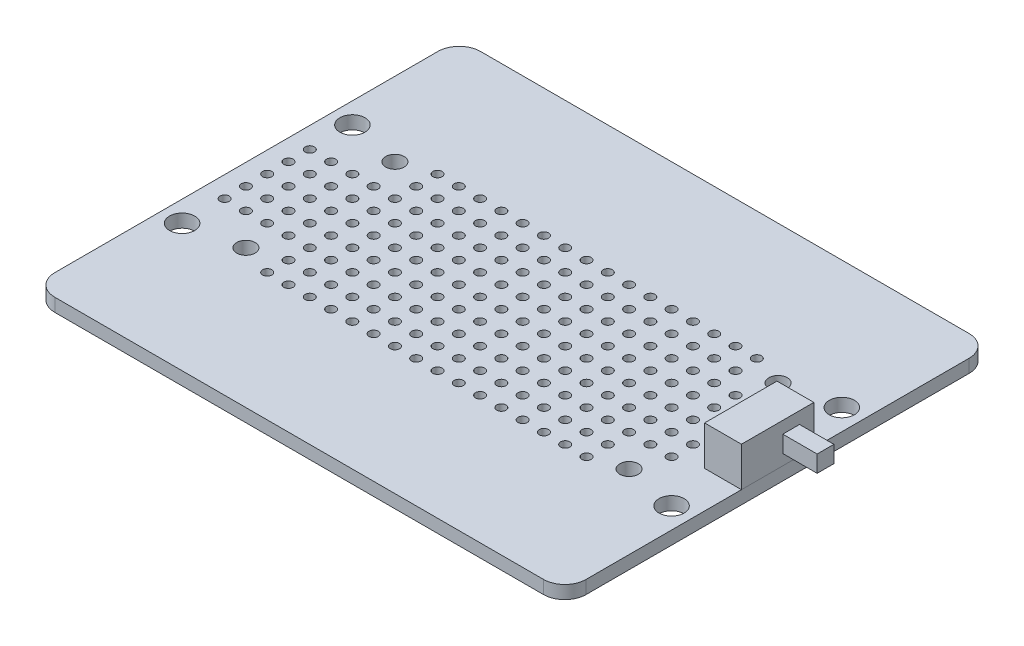
SolidWorks part; units mm, degrees
ref_plane "Front" through (0, 0, 0) normal (0, 0, 1) x (1, 0, 0)
ref_plane "Top" through (0, 0, 0) normal (0, 1, 0) x (1, 0, 0)
ref_plane "Right" through (0, 0, 0) normal (1, 0, 0) x (0, 0, -1)
sketch "Sketch1" plane through (0, 0, 0) normal (0, 1, 0) x (1, 0, 0)
  line L0 (29.2, 10.16) -> (29.2, -10.16) construction
  line L1 (-31.7, 25.4) -> (31.7, 25.4)
  line L2 (-31.7, 25.4) -> (-31.7, -25.4)
  line L3 (-31.7, -25.4) -> (31.7, -25.4)
  line L4 (31.7, 25.4) -> (31.7, -25.4)
  line L5 (-31.7, 25.4) -> (31.7, -25.4) construction
  line L6 (-31.7, -25.4) -> (31.7, 25.4) construction
  line L7 (29.2, 0) -> (0, 0) construction
  line L8 (-29.2, 10.16) -> (-29.2, -10.16) construction
  line L9 (-29.2, 0) -> (0, 0) construction
  line L10 (-22.86, 8.89) -> (-22.86, -8.89) construction
  line L11 (22.86, 8.89) -> (22.86, -8.89) construction
  line L12 (-22.86, 0) -> (22.86, 0) construction
  circle A0 centre (29.2, 10.16) radius 1.5
  circle A1 centre (29.2, -10.16) radius 1.5
  circle A2 centre (-29.2, 10.16) radius 1.5
  circle A3 centre (-29.2, -10.16) radius 1.5
  circle A4 centre (-22.86, 8.89) radius 1.1
  circle A5 centre (-22.86, -8.89) radius 1.1
  circle A6 centre (22.86, -8.89) radius 1.1
  circle A7 centre (22.86, 8.89) radius 1.1
  point P0 (0, 0)
  point P29 (0, 0)
  dimension "D3" = 3
  dimension "D4" = 20.32
  dimension "D5" = 55.4
  dimension "D6" = 2.2
  dimension "D1" = 50.8
  dimension "D2" = 63.4
  dimension "D7" = 45.72
  dimension "D8" = 17.78
  dimension "D9" = 17.78
extrude "Boss-Extrude1" add sketch "Sketch1" along normal blind 1.57
sketch "Sketch9" plane through (0, 0, 0) normal (0, 1, 0) x (1, 0, 0)
  line L0 (-29.21, 10.16) -> (-26.67, 10.16) construction
  line L1 (-29.21, 10.16) -> (-29.21, 7.62) construction
  line L2 (-29.21, 10.16) -> (24.13, 10.16) construction
  line L3 (24.13, 10.16) -> (24.13, -10.16) construction
  line L4 (24.13, -10.16) -> (-29.21, -10.16) construction
  line L5 (-29.21, -10.16) -> (-29.21, 10.16) construction
  line L6 (-2.54, 10.16) -> (-2.54, -10.16) construction
  line L7 (-29.21, 0) -> (24.13, 0) construction
  circle A0 centre (-29.21, 10.16) radius 0.55
  circle A1 centre (-26.67, 10.16) radius 0.55 [skipped]
  circle A2 centre (-24.13, 10.16) radius 0.55 [skipped]
  circle A3 centre (-21.59, 10.16) radius 0.55 [skipped]
  circle A4 centre (-19.05, 10.16) radius 0.55
  circle A5 centre (-16.51, 10.16) radius 0.55
  circle A6 centre (-13.97, 10.16) radius 0.55
  circle A7 centre (-11.43, 10.16) radius 0.55
  circle A8 centre (-8.89, 10.16) radius 0.55
  circle A9 centre (-6.35, 10.16) radius 0.55
  circle A10 centre (-3.81, 10.16) radius 0.55
  circle A11 centre (-1.27, 10.16) radius 0.55
  circle A12 centre (1.27, 10.16) radius 0.55
  circle A13 centre (3.81, 10.16) radius 0.55
  circle A14 centre (6.35, 10.16) radius 0.55
  circle A15 centre (8.89, 10.16) radius 0.55
  circle A16 centre (11.43, 10.16) radius 0.55
  circle A17 centre (13.97, 10.16) radius 0.55
  circle A18 centre (16.51, 10.16) radius 0.55
  circle A19 centre (19.05, 10.16) radius 0.55
  circle A20 centre (21.59, 10.16) radius 0.55 [skipped]
  circle A21 centre (24.13, 10.16) radius 0.55 [skipped]
  circle A22 centre (26.67, 10.16) radius 0.55 [skipped]
  circle A23 centre (29.21, 10.16) radius 0.55 [skipped]
  circle A24 centre (-26.67, 7.62) radius 0.55 [skipped]
  circle A25 centre (-24.13, 7.62) radius 0.55 [skipped]
  circle A26 centre (-21.59, 7.62) radius 0.55 [skipped]
  circle A27 centre (-19.05, 7.62) radius 0.55
  circle A28 centre (-16.51, 7.62) radius 0.55
  circle A29 centre (-13.97, 7.62) radius 0.55
  circle A30 centre (-11.43, 7.62) radius 0.55
  circle A31 centre (-8.89, 7.62) radius 0.55
  circle A32 centre (-6.35, 7.62) radius 0.55
  circle A33 centre (-3.81, 7.62) radius 0.55
  circle A34 centre (-1.27, 7.62) radius 0.55
  circle A35 centre (1.27, 7.62) radius 0.55
  circle A36 centre (3.81, 7.62) radius 0.55
  circle A37 centre (6.35, 7.62) radius 0.55
  circle A38 centre (8.89, 7.62) radius 0.55
  circle A39 centre (11.43, 7.62) radius 0.55
  circle A40 centre (13.97, 7.62) radius 0.55
  circle A41 centre (16.51, 7.62) radius 0.55
  circle A42 centre (19.05, 7.62) radius 0.55
  circle A43 centre (21.59, 7.62) radius 0.55 [skipped]
  circle A44 centre (24.13, 7.62) radius 0.55 [skipped]
  circle A45 centre (26.67, 7.62) radius 0.55 [skipped]
  circle A46 centre (29.21, 7.62) radius 0.55 [skipped]
  circle A47 centre (-26.67, 5.08) radius 0.55
  circle A48 centre (-24.13, 5.08) radius 0.55
  circle A49 centre (-21.59, 5.08) radius 0.55
  circle A50 centre (-19.05, 5.08) radius 0.55
  circle A51 centre (-16.51, 5.08) radius 0.55
  circle A52 centre (-13.97, 5.08) radius 0.55
  circle A53 centre (-11.43, 5.08) radius 0.55
  circle A54 centre (-8.89, 5.08) radius 0.55
  circle A55 centre (-6.35, 5.08) radius 0.55
  circle A56 centre (-3.81, 5.08) radius 0.55
  circle A57 centre (-1.27, 5.08) radius 0.55
  circle A58 centre (1.27, 5.08) radius 0.55
  circle A59 centre (3.81, 5.08) radius 0.55
  circle A60 centre (6.35, 5.08) radius 0.55
  circle A61 centre (8.89, 5.08) radius 0.55
  circle A62 centre (11.43, 5.08) radius 0.55
  circle A63 centre (13.97, 5.08) radius 0.55
  circle A64 centre (16.51, 5.08) radius 0.55
  circle A65 centre (19.05, 5.08) radius 0.55
  circle A66 centre (21.59, 5.08) radius 0.55
  circle A67 centre (24.13, 5.08) radius 0.55
  circle A68 centre (26.67, 5.08) radius 0.55 [skipped]
  circle A69 centre (29.21, 5.08) radius 0.55 [skipped]
  circle A70 centre (-26.67, 2.54) radius 0.55
  circle A71 centre (-24.13, 2.54) radius 0.55
  circle A72 centre (-21.59, 2.54) radius 0.55
  circle A73 centre (-19.05, 2.54) radius 0.55
  circle A74 centre (-16.51, 2.54) radius 0.55
  circle A75 centre (-13.97, 2.54) radius 0.55
  circle A76 centre (-11.43, 2.54) radius 0.55
  circle A77 centre (-8.89, 2.54) radius 0.55
  circle A78 centre (-6.35, 2.54) radius 0.55
  circle A79 centre (-3.81, 2.54) radius 0.55
  circle A80 centre (-1.27, 2.54) radius 0.55
  circle A81 centre (1.27, 2.54) radius 0.55
  circle A82 centre (3.81, 2.54) radius 0.55
  circle A83 centre (6.35, 2.54) radius 0.55
  circle A84 centre (8.89, 2.54) radius 0.55
  circle A85 centre (11.43, 2.54) radius 0.55
  circle A86 centre (13.97, 2.54) radius 0.55
  circle A87 centre (16.51, 2.54) radius 0.55
  circle A88 centre (19.05, 2.54) radius 0.55
  circle A89 centre (21.59, 2.54) radius 0.55
  circle A90 centre (24.13, 2.54) radius 0.55
  circle A91 centre (26.67, 2.54) radius 0.55 [skipped]
  circle A92 centre (29.21, 2.54) radius 0.55 [skipped]
  circle A93 centre (-26.67, 0) radius 0.55
  circle A94 centre (-24.13, 0) radius 0.55
  circle A95 centre (-21.59, 0) radius 0.55
  circle A96 centre (-19.05, 0) radius 0.55
  circle A97 centre (-16.51, 0) radius 0.55
  circle A98 centre (-13.97, 0) radius 0.55
  circle A99 centre (-11.43, 0) radius 0.55
  circle A100 centre (-8.89, 0) radius 0.55
  circle A101 centre (-6.35, 0) radius 0.55
  circle A102 centre (-3.81, 0) radius 0.55
  circle A103 centre (-1.27, 0) radius 0.55
  circle A104 centre (1.27, 0) radius 0.55
  circle A105 centre (3.81, 0) radius 0.55
  circle A106 centre (6.35, 0) radius 0.55
  circle A107 centre (8.89, 0) radius 0.55
  circle A108 centre (11.43, 0) radius 0.55
  circle A109 centre (13.97, 0) radius 0.55
  circle A110 centre (16.51, 0) radius 0.55
  circle A111 centre (19.05, 0) radius 0.55
  circle A112 centre (21.59, 0) radius 0.55
  circle A113 centre (24.13, 0) radius 0.55
  circle A114 centre (26.67, 0) radius 0.55 [skipped]
  circle A115 centre (29.21, 0) radius 0.55 [skipped]
  circle A116 centre (-26.67, -2.54) radius 0.55
  circle A117 centre (-24.13, -2.54) radius 0.55
  circle A118 centre (-21.59, -2.54) radius 0.55
  circle A119 centre (-19.05, -2.54) radius 0.55
  circle A120 centre (-16.51, -2.54) radius 0.55
  circle A121 centre (-13.97, -2.54) radius 0.55
  circle A122 centre (-11.43, -2.54) radius 0.55
  circle A123 centre (-8.89, -2.54) radius 0.55
  circle A124 centre (-6.35, -2.54) radius 0.55
  circle A125 centre (-3.81, -2.54) radius 0.55
  circle A126 centre (-1.27, -2.54) radius 0.55
  circle A127 centre (1.27, -2.54) radius 0.55
  circle A128 centre (3.81, -2.54) radius 0.55
  circle A129 centre (6.35, -2.54) radius 0.55
  circle A130 centre (8.89, -2.54) radius 0.55
  circle A131 centre (11.43, -2.54) radius 0.55
  circle A132 centre (13.97, -2.54) radius 0.55
  circle A133 centre (16.51, -2.54) radius 0.55
  circle A134 centre (19.05, -2.54) radius 0.55
  circle A135 centre (21.59, -2.54) radius 0.55
  circle A136 centre (24.13, -2.54) radius 0.55
  circle A137 centre (26.67, -2.54) radius 0.55 [skipped]
  circle A138 centre (29.21, -2.54) radius 0.55 [skipped]
  circle A139 centre (-26.67, -5.08) radius 0.55
  circle A140 centre (-24.13, -5.08) radius 0.55
  circle A141 centre (-21.59, -5.08) radius 0.55
  circle A142 centre (-19.05, -5.08) radius 0.55
  circle A143 centre (-16.51, -5.08) radius 0.55
  circle A144 centre (-13.97, -5.08) radius 0.55
  circle A145 centre (-11.43, -5.08) radius 0.55
  circle A146 centre (-8.89, -5.08) radius 0.55
  circle A147 centre (-6.35, -5.08) radius 0.55
  circle A148 centre (-3.81, -5.08) radius 0.55
  circle A149 centre (-1.27, -5.08) radius 0.55
  circle A150 centre (1.27, -5.08) radius 0.55
  circle A151 centre (3.81, -5.08) radius 0.55
  circle A152 centre (6.35, -5.08) radius 0.55
  circle A153 centre (8.89, -5.08) radius 0.55
  circle A154 centre (11.43, -5.08) radius 0.55
  circle A155 centre (13.97, -5.08) radius 0.55
  circle A156 centre (16.51, -5.08) radius 0.55
  circle A157 centre (19.05, -5.08) radius 0.55
  circle A158 centre (21.59, -5.08) radius 0.55
  circle A159 centre (24.13, -5.08) radius 0.55
  circle A160 centre (26.67, -5.08) radius 0.55 [skipped]
  circle A161 centre (29.21, -5.08) radius 0.55 [skipped]
  circle A162 centre (-26.67, -7.62) radius 0.55 [skipped]
  circle A163 centre (-24.13, -7.62) radius 0.55 [skipped]
  circle A164 centre (-21.59, -7.62) radius 0.55 [skipped]
  circle A165 centre (-19.05, -7.62) radius 0.55
  circle A166 centre (-16.51, -7.62) radius 0.55
  circle A167 centre (-13.97, -7.62) radius 0.55
  circle A168 centre (-11.43, -7.62) radius 0.55
  circle A169 centre (-8.89, -7.62) radius 0.55
  circle A170 centre (-6.35, -7.62) radius 0.55
  circle A171 centre (-3.81, -7.62) radius 0.55
  circle A172 centre (-1.27, -7.62) radius 0.55
  circle A173 centre (1.27, -7.62) radius 0.55
  circle A174 centre (3.81, -7.62) radius 0.55
  circle A175 centre (6.35, -7.62) radius 0.55
  circle A176 centre (8.89, -7.62) radius 0.55
  circle A177 centre (11.43, -7.62) radius 0.55
  circle A178 centre (13.97, -7.62) radius 0.55
  circle A179 centre (16.51, -7.62) radius 0.55
  circle A180 centre (19.05, -7.62) radius 0.55
  circle A181 centre (21.59, -7.62) radius 0.55 [skipped]
  circle A182 centre (24.13, -7.62) radius 0.55 [skipped]
  circle A183 centre (26.67, -7.62) radius 0.55 [skipped]
  circle A184 centre (29.21, -7.62) radius 0.55 [skipped]
  circle A185 centre (-26.67, -10.16) radius 0.55 [skipped]
  circle A186 centre (-24.13, -10.16) radius 0.55 [skipped]
  circle A187 centre (-21.59, -10.16) radius 0.55 [skipped]
  circle A188 centre (-19.05, -10.16) radius 0.55
  circle A189 centre (-16.51, -10.16) radius 0.55
  circle A190 centre (-13.97, -10.16) radius 0.55
  circle A191 centre (-11.43, -10.16) radius 0.55
  circle A192 centre (-8.89, -10.16) radius 0.55
  circle A193 centre (-6.35, -10.16) radius 0.55
  circle A194 centre (-3.81, -10.16) radius 0.55
  circle A195 centre (-1.27, -10.16) radius 0.55
  circle A196 centre (1.27, -10.16) radius 0.55
  circle A197 centre (3.81, -10.16) radius 0.55
  circle A198 centre (6.35, -10.16) radius 0.55
  circle A199 centre (8.89, -10.16) radius 0.55
  circle A200 centre (11.43, -10.16) radius 0.55
  circle A201 centre (13.97, -10.16) radius 0.55
  circle A202 centre (16.51, -10.16) radius 0.55
  circle A203 centre (19.05, -10.16) radius 0.55
  circle A204 centre (21.59, -10.16) radius 0.55 [skipped]
  circle A205 centre (24.13, -10.16) radius 0.55 [skipped]
  circle A206 centre (26.67, -10.16) radius 0.55 [skipped]
  circle A207 centre (29.21, -10.16) radius 0.55 [skipped]
  circle A208 centre (-29.21, 7.62) radius 0.55 [skipped]
  circle A209 centre (-29.21, 5.08) radius 0.55
  circle A210 centre (-29.21, 2.54) radius 0.55
  circle A211 centre (-29.21, 0) radius 0.55
  circle A212 centre (-29.21, -2.54) radius 0.55
  circle A213 centre (-29.21, -5.08) radius 0.55
  circle A214 centre (-29.21, -7.62) radius 0.55 [skipped]
  circle A215 centre (-29.21, -10.16) radius 0.55 [skipped]
  dimension "D1" = 1.1
  dimension "D4" = 2.54
  dimension "D5" = 2.54
  dimension "D6" = 2.54
  dimension "D2" = 24
  dimension "D3" = 9
extrude "Cut-Extrude1" cut sketch "Sketch9" along normal through all
sketch "Sketch7" plane through (0, 1.57, 0) normal (0, 1, 0) x (1, 0, 0)
  line L0 (31.7, -25.4) -> (31.7, 25.4) construction
  line L1 (31.7, 4.32) -> (27.3, 4.32)
  line L2 (31.7, 4.32) -> (31.7, -4.32)
  line L3 (31.7, -4.32) -> (27.3, -4.32)
  line L4 (27.3, 4.32) -> (27.3, -4.32)
  line L5 (27.3, 0) -> (0, 0) construction
  dimension "D1" = 4.4
  dimension "D2" = 8.64
extrude "Boss-Extrude6" add sketch "Sketch7" along normal blind 4.7 separate body
sketch "Sketch8" plane through (31.7, 0, 0) normal (1, 0, 0) x (0, 0, -1)
  line L1 (0.6103, 4.843) -> (2.6103, 4.843)
  line L2 (0.6103, 4.843) -> (0.6103, 2.843)
  line L3 (0.6103, 2.843) -> (2.6103, 2.843)
  line L4 (2.6103, 4.843) -> (2.6103, 2.843)
  dimension "D1" = 2
  dimension "D2" = 2
extrude "Boss-Extrude7" add sketch "Sketch8" along normal blind 4.1 separate body
fillet "Fillet1" radius 2.54 4 edges at (-31.7, 0.785, -25.4) (-31.7, 0.785, 25.4) (31.7, 0.785, -25.4) (31.7, 0.785, 25.4)
